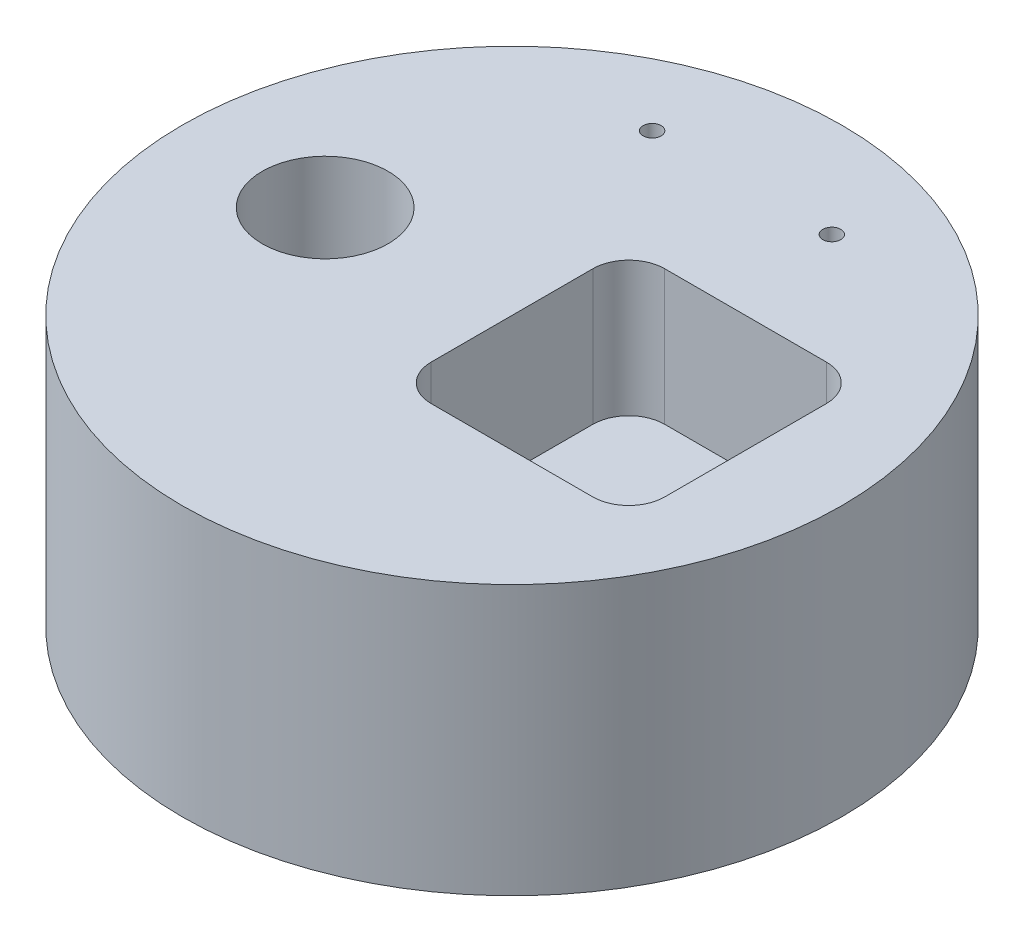
SolidWorks part; units mm, degrees
ref_plane "Front Plane" through (0, 0, 0) normal (0, 0, 1) x (1, 0, 0)
ref_plane "Top Plane" through (0, 0, 0) normal (0, 1, 0) x (1, 0, 0)
ref_plane "Right Plane" through (0, 0, 0) normal (1, 0, 0) x (0, 0, -1)
sketch "Sketch1" plane through (0, 0, 0) normal (0, 1, 0) x (1, 0, 0)
  circle A0 centre (0, 0) radius 46.609
  dimension "D1" = 93.218
extrude "Boss-Extrude1" add sketch "Sketch1" along normal blind 38.1
sketch "Sketch2" plane through (0, 38.1, 0) normal (0, 1, 0) x (1, 0, 0)
  circle A0 centre (0, 32.512) radius 4.9824
  circle A1 centre (12.7, 32.512) radius 1.27
  circle A2 centre (-12.7, 32.512) radius 1.27
  dimension "D4" = 2.54
  dimension "D5" = 2.54
  dimension "D1" = 32.512
  dimension "D2" = 0
  dimension "D3" = 0
  dimension "D6" = 12.7
  dimension "D7" = 12.7
extrude "Cut-Extrude1" cut sketch "Sketch2" against normal up to surface (38.1 mm away) contours A1 | A2 up to face at (0, 0, 46.609)
sketch "Sketch3" plane through (0, 38.1, 0) normal (0, 1, 0) x (1, 0, 0)
  circle A0 centre (-26.41, 0) radius 8.89
  dimension "D1" = 17.78
extrude "Cut-Extrude2" cut sketch "Sketch3" against normal up to surface (38.1 mm away) up to face at (12.7, 0, -31.242)
sketch "Sketch4" plane through (0, 38.1, 0) normal (0, 1, 0) x (1, 0, 0)
  line L1 (0, 16.51) -> (33.02, 16.51)
  line L2 (0, 16.51) -> (0, -16.51)
  line L3 (0, -16.51) -> (33.02, -16.51)
  line L4 (33.02, 16.51) -> (33.02, -16.51)
  point P4 (0, 0)
  dimension "D1" = 0
  dimension "D2" = 33.02
  dimension "D4" = 33.02
  dimension "D5" = 0
extrude "Cut-Extrude3" cut sketch "Sketch4" against normal blind 19.05
fillet "Fillet1" radius 5.08 4 edges at (0, 28.575, 16.51) (33.02, 28.575, 16.51) (33.02, 28.575, -16.51) (0, 28.575, -16.51)
